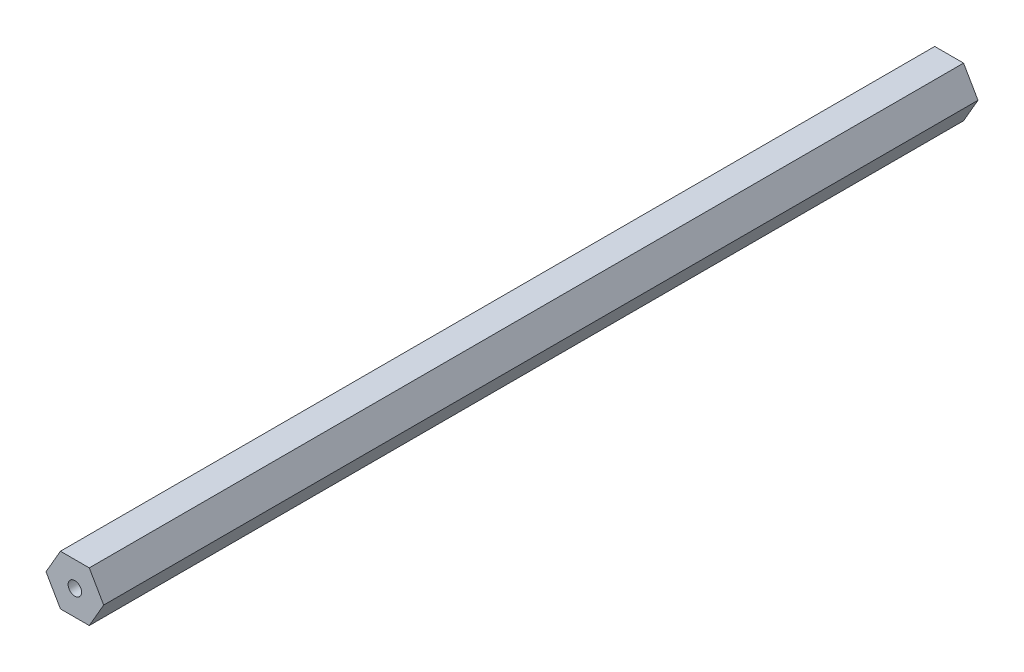
SolidWorks part; units mm, degrees
material "7075-T6 (SN)"
ref_plane "Front Plane" through (0, 0, 0) normal (0, 0, 1) x (1, 0, 0)
ref_plane "Top Plane" through (0, 0, 0) normal (0, 1, 0) x (1, 0, 0)
ref_plane "Right Plane" through (0, 0, 0) normal (1, 0, 0) x (0, 0, -1)
other "Configuration Table"
sketch "Sketch1" plane through (0, 0, 0) normal (0, 0, 1) x (1, 0, 0)
  line L1 (7.3323, 0) -> (3.6662, 6.35)
  line L2 (3.6662, 6.35) -> (-3.6662, 6.35)
  line L3 (-3.6662, 6.35) -> (-7.3323, 0)
  line L4 (-7.3323, 0) -> (-3.6662, -6.35)
  line L5 (-3.6662, -6.35) -> (3.6662, -6.35)
  line L6 (3.6662, -6.35) -> (7.3323, 0)
  circle A0 centre (0, 0) radius 6.35 construction
  circle A1 centre (0, 0) radius 1.7145
  dimension "D2" = 3.429
  dimension "D1" = 12.7
extrude "Boss-Extrude1" add sketch "Sketch1" along normal blind 222.25
equation "\"length\"= 8.75"
equation "\"D1@Boss-Extrude1\"=\"length\""
